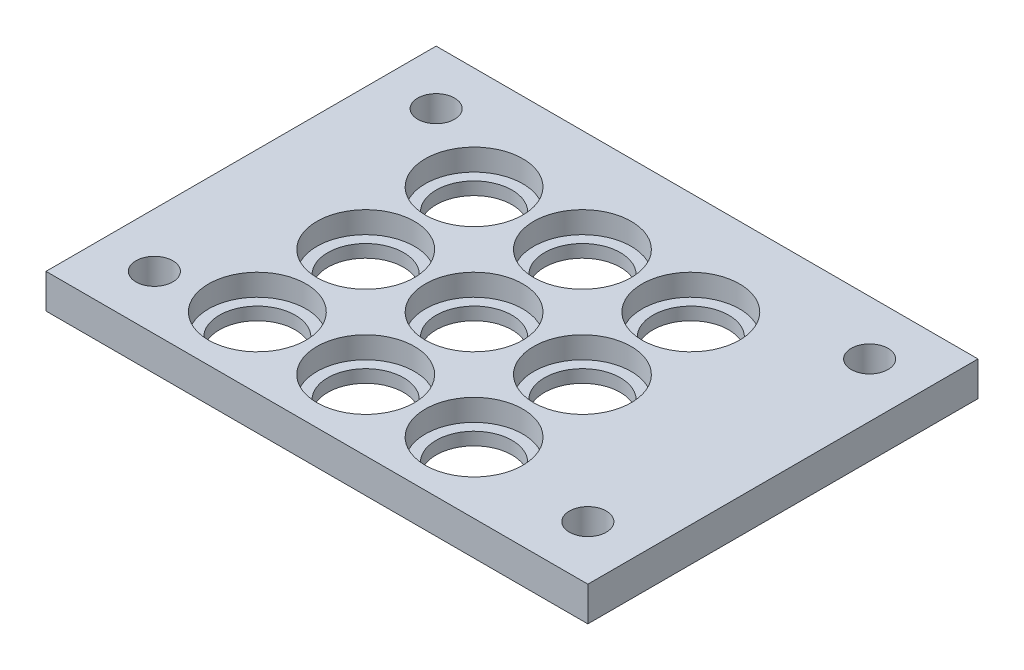
SolidWorks part; units mm, degrees
ref_plane "Front Plane" through (0, 0, 0) normal (0, 0, 1) x (1, 0, 0)
ref_plane "Top Plane" through (0, 0, 0) normal (0, 1, 0) x (1, 0, 0)
ref_plane "Right Plane" through (0, 0, 0) normal (1, 0, 0) x (0, 0, -1)
sketch "Sketch1" plane through (0, 0, 0) normal (0, 1, 0) x (1, 0, 0)
  line L0 (45, 31) -> (5, 31) construction
  line L1 (0, 0) -> (50, 0)
  line L2 (0, 0) -> (0, 36)
  line L3 (0, 36) -> (50, 36)
  line L4 (50, 0) -> (50, 36)
  line L6 (45, 31) -> (45, 5) construction
  circle A19 centre (13, 6.5) radius 3.5
  circle A28 centre (5, 5) radius 1.7
  circle A29 centre (5, 31) radius 1.7
  circle A30 centre (45, 31) radius 1.7
  circle A31 centre (45, 5) radius 1.7
  circle A32 centre (23, 6.5) radius 3.5
  circle A33 centre (33, 6.5) radius 3.5
  circle A34 centre (23, 16.5) radius 3.5
  circle A35 centre (33, 16.5) radius 3.5
  circle A36 centre (23, 26.5) radius 3.5
  circle A37 centre (33, 26.5) radius 3.5
  circle A38 centre (13, 16.5) radius 3.5
  circle A39 centre (13, 26.5) radius 3.5
  point P7 (45, 18)
  point P9 (25, 31)
  point P10 (25, 36)
  point P20 (50, 18)
  dimension "D5" = 40
  dimension "D6" = 26
  dimension "D3" = 7
  dimension "D8" = 3.4
  dimension "D1" = 50
  dimension "D2" = 36
  dimension "D4" = 8
  dimension "D7" = 1.5
  dimension "D9" = 3
extrude "Boss-Extrude1" add sketch "Sketch1" along normal blind 3.175
sketch "Sketch2" plane through (0, 3.175, 0) normal (0, 1, 0) x (1, 0, 0)
  circle A0 centre (13, 26.5) radius 4.5
  circle A1 centre (13, 26.5) radius 3.5 construction
  circle A2 centre (23, 26.5) radius 4.5
  circle A3 centre (33, 26.5) radius 4.5
  circle A4 centre (23, 16.5) radius 4.5
  circle A5 centre (33, 16.5) radius 4.5
  circle A6 centre (23, 6.5) radius 4.5
  circle A7 centre (33, 6.5) radius 4.5
  circle A8 centre (13, 16.5) radius 4.5
  circle A9 centre (13, 6.5) radius 4.5
  dimension "D1" = 9
  dimension "D2" = 3
extrude "Cut-Extrude1" cut sketch "Sketch2" against normal blind 2
equation "\"o\"= 10mm"
equation "\"P\"= 10"
